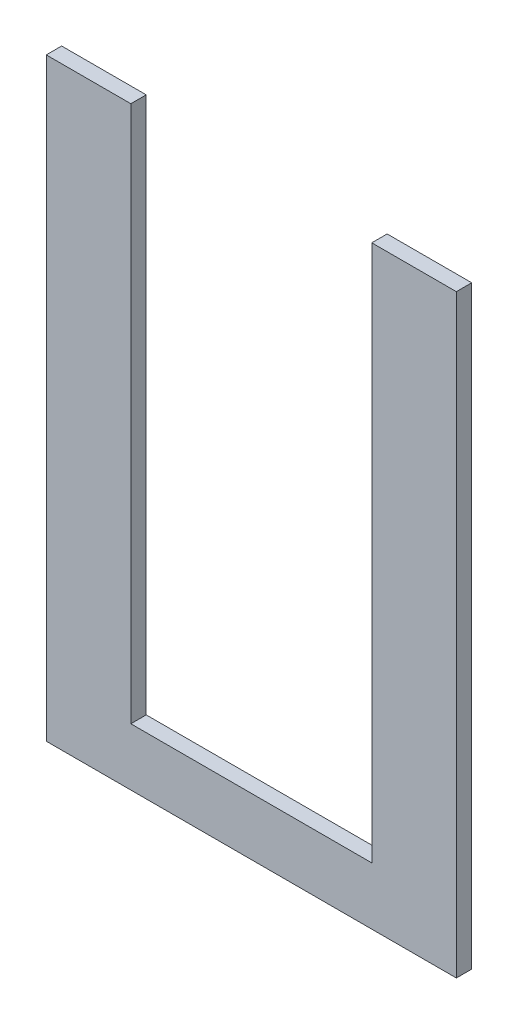
SolidWorks part; units mm, degrees
ref_plane "Front Plane" through (0, 0, 0) normal (0, 0, 1) x (1, 0, 0)
ref_plane "Top Plane" through (0, 0, 0) normal (0, 1, 0) x (1, 0, 0)
ref_plane "Right Plane" through (0, 0, 0) normal (1, 0, 0) x (0, 0, -1)
sketch "Sketch1" plane through (0, 0, 0) normal (0, 0, 1) x (1, 0, 0)
  line L0 (16.5, 115.957) -> (16.5, 11.2)
  line L1 (0, 0) -> (80, 0)
  line L2 (0, 0) -> (0, 115.957)
  line L3 (0, 115.957) -> (80, 115.957) construction
  line L4 (80, 0) -> (80, 115.957)
  line L5 (16.5, 11.2) -> (63.5, 11.2)
  line L6 (63.5, 11.2) -> (63.5, 115.957)
  line L7 (63.5, 115.957) -> (80, 115.957)
  line L8 (16.5, 115.957) -> (0, 115.957)
  line L9 (40, 115.957) -> (40, 0) construction
sketch "Sketch2" plane through (0, 0, 0) normal (0, 1, 0) x (1, 0, 0)
  line L1 (0, 0) -> (80, 0)
  line L2 (0, 0) -> (0, 3)
  line L3 (0, 3) -> (80, 3)
  line L4 (80, 0) -> (80, 3)
extrude "Boss-Extrude1" add sketch "Sketch1" against normal up to vertex (3 mm away) up to point (0, 0, -3)
